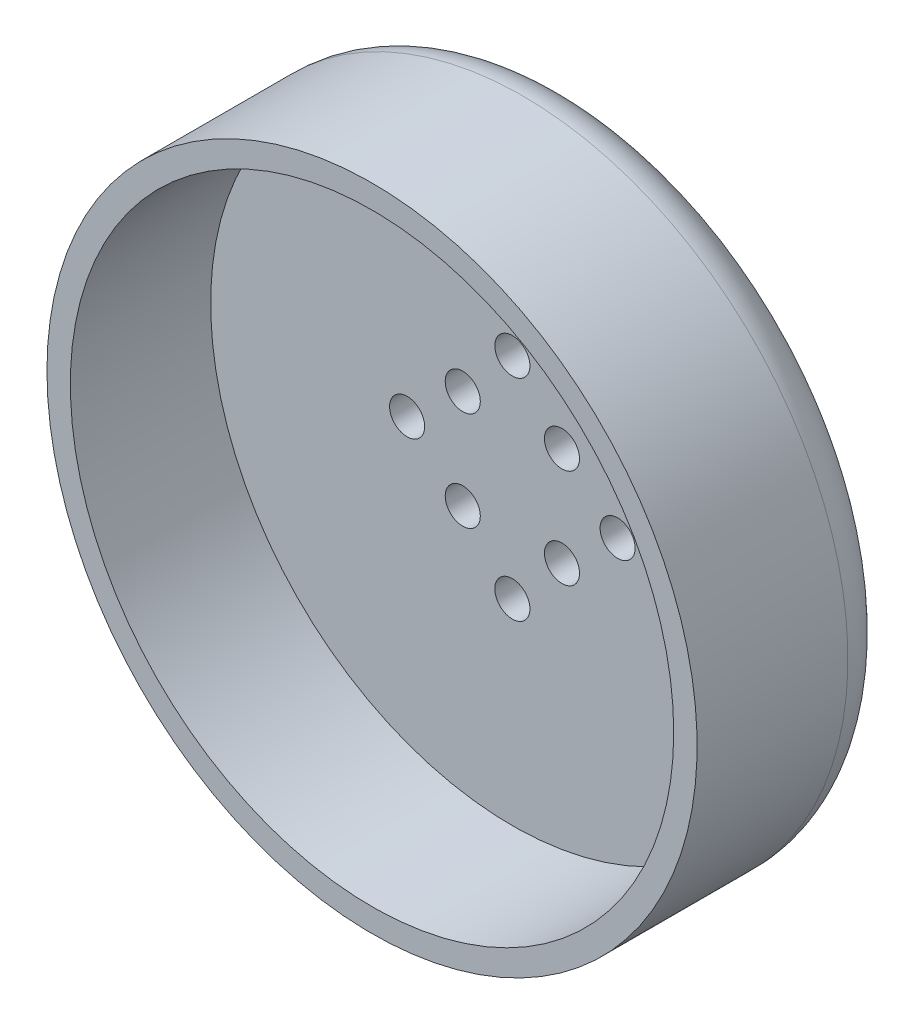
SolidWorks part; units mm, degrees
ref_plane "Front Plane" through (0, 0, 0) normal (0, 0, 1) x (1, 0, 0)
ref_plane "Top Plane" through (0, 0, 0) normal (0, 1, 0) x (1, 0, 0)
ref_plane "Right Plane" through (0, 0, 0) normal (1, 0, 0) x (0, 0, -1)
ref_axis "Axis1" through (0, 0, -88.99) along (0, 0, 1)
sketch "Sketch2" plane through (0, 0, 0) normal (0, 1, 0) x (1, 0, 0)
  line L0 (0, 32) -> (-2, 32)
  line L1 (0, 88.99) -> (0, -88.99) construction
  line L2 (-2, 32) -> (-2, 27)
  line L3 (-2, 27) -> (-27.8, 27)
  line L4 (-27.8, 27) -> (-27.8, 8.25)
  line L5 (-27.8, 8.25) -> (0, 8.25)
  line L6 (0, 8.25) -> (0, 32)
  dimension "D1" = 2
  dimension "D2" = 27.8
  dimension "D3" = 32
  dimension "D4" = 27
  dimension "D5" = 8.25
revolve "Revolve1" add sketch "Sketch2" angle 360 about axis through (0, 0, -88.99) along (0, 0, 1)
sketch "Sketch3" plane through (0, 0, -27) normal (0, 0, -1) x (-1, 0, 0)
  line L0 (0, 0) -> (0, 50000) construction
  line L1 (0, 0) -> (50000, 0) construction
  line L2 (0, 9) -> (0, 0) construction
  line L3 (0, 0) -> (4.2426, 4.2426) construction
  circle A0 centre (0, 9) radius 1.5
  circle A1 centre (4.2426, 4.2426) radius 1.5
  dimension "D4" = 3
  dimension "D5" = 3
  dimension "D1" = 45
  dimension "D2" = 6
  dimension "D3" = 9
extrude "Cut-Extrude1" cut sketch "Sketch3" against normal through all
pattern_circular "CirPattern1" count 4 over 360 about axis through (0, 0, 0) along (0, 0, 1) of "Cut-Extrude1"
chamfer "Chamfer1" distance 2.5 angle 80 1 edges at (-27.8, 0, -27)
fillet "Fillet1" radius 4 1 edges at (-27.8, 0, -24.5)
sketch "Sketch4" plane through (0, 0, -8.25) normal (0, 0, 1) x (1, 0, 0)
  circle A0 centre (0, 0) radius 25.8
  circle A1 centre (0, 0) radius 27.8 construction
  dimension "D1" = 2
extrude "Cut-Extrude2" cut sketch "Sketch4" against normal blind 12
